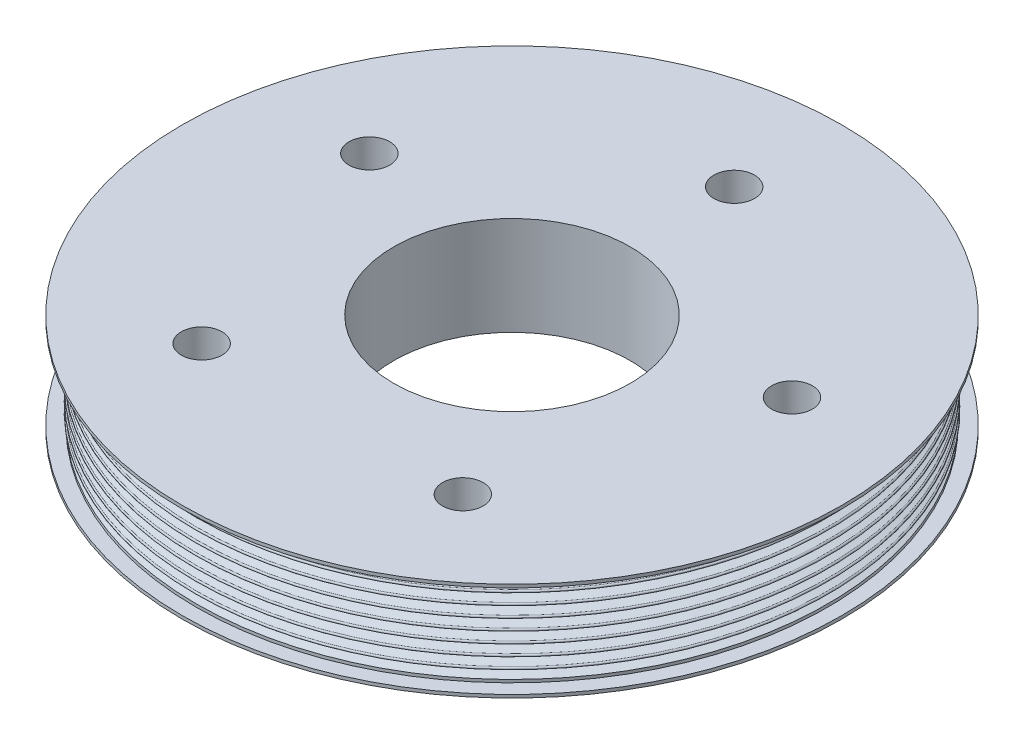
SolidWorks part; units mm, degrees
material "6061-T6 (SS)"
ref_plane "Front Plane" through (0, 0, 0) normal (0, 0, 1) x (1, 0, 0)
ref_plane "Top Plane" through (0, 0, 0) normal (0, 1, 0) x (1, 0, 0)
ref_plane "Right Plane" through (0, 0, 0) normal (1, 0, 0) x (0, 0, -1)
sketch "Sketch1" plane through (0, 0, 0) normal (0, 0, 1) x (1, 0, 0)
  line L0 (101.6, 13.904) -> (101.6, 14.8565)
  line L1 (101.6, -13.904) -> (101.6, -14.8565)
  line L2 (106.172, -15.8725) -> (101.6, -15.8725)
  line L3 (101.6, -13.904) -> (98.7876, -12.8803)
  line L4 (98.7876, -12.8803) -> (98.7876, -12.1183) construction
  line L5 (98.7876, -12.1183) -> (101.6, -11.0947)
  line L6 (101.6, -11.0947) -> (101.6, -10.3327) construction
  line L7 (101.6, -10.3327) -> (98.7876, -9.3091)
  line L8 (98.7876, -9.3091) -> (98.7876, -8.5471) construction
  line L9 (98.7876, -8.5471) -> (101.6, -7.5235)
  line L10 (101.6, -7.5235) -> (101.6, -6.7615) construction
  line L11 (101.6, -6.7615) -> (98.7876, -5.7379)
  line L12 (98.7876, -5.7379) -> (98.7876, -4.9759) construction
  line L13 (98.7876, -4.9759) -> (101.6, -3.9522)
  line L14 (101.6, -3.9522) -> (101.6, -3.1902) construction
  line L15 (101.6, -3.1902) -> (98.7876, -2.1666)
  line L16 (98.7876, -2.1666) -> (98.7876, -1.4046) construction
  line L17 (98.7876, -1.4046) -> (101.6, -0.381)
  line L18 (101.6, -0.381) -> (101.6, 0.381) construction
  line L19 (101.6, 0.381) -> (98.7876, 1.4046)
  line L20 (98.7876, 1.4046) -> (98.7876, 2.1666) construction
  line L21 (98.7876, 2.1666) -> (101.6, 3.1902)
  line L22 (101.6, 3.1902) -> (101.6, 3.9522) construction
  line L23 (101.6, 3.9522) -> (98.7876, 4.9759)
  line L24 (98.7876, 4.9759) -> (98.7876, 5.7379) construction
  line L25 (98.7876, 5.7379) -> (101.6, 6.7615)
  line L26 (101.6, 6.7615) -> (101.6, 7.5235) construction
  line L27 (101.6, 7.5235) -> (98.7876, 8.5471)
  line L28 (98.7876, 8.5471) -> (98.7876, 9.3091) construction
  line L29 (98.7876, 9.3091) -> (101.6, 10.3327)
  line L30 (101.6, 10.3327) -> (101.6, 11.0947) construction
  line L31 (101.6, 11.0947) -> (98.7876, 12.1183)
  line L32 (98.7876, 12.1183) -> (98.7876, 12.8803) construction
  line L33 (98.7876, 12.8803) -> (101.6, 13.904)
  line L34 (101.6, -15.8725) -> (0, -15.8725)
  line L35 (101.6, 15.8725) -> (0, 15.8725)
  line L36 (0, 15.8725) -> (0, -15.8725)
  line L37 (101.6, 10.7137) -> (23.534, 10.7137) construction
  line L38 (101.6, -13.904) -> (101.6, -11.0947) construction
  line L39 (106.172, -15.8725) -> (106.172, -14.8565)
  line L40 (106.172, -14.8565) -> (101.6, -14.8565)
  line L42 (101.6, 15.8725) -> (106.172, 15.8725)
  line L43 (106.172, 15.8725) -> (106.172, 14.8565)
  line L44 (106.172, 14.8565) -> (101.6, 14.8565)
  arc A0 (98.7876, 12.8803) -> (98.7876, 12.1183) centre (98.7876, 12.4993) ccw
  arc A1 (98.7876, 9.3091) -> (98.7876, 8.5471) centre (98.7876, 8.9281) ccw
  arc A2 (98.7876, 5.7379) -> (98.7876, 4.9759) centre (98.7876, 5.3569) ccw
  arc A3 (98.7876, 2.1666) -> (98.7876, 1.4046) centre (98.7876, 1.7856) ccw
  arc A4 (98.7876, -1.4046) -> (98.7876, -2.1666) centre (98.7876, -1.7856) ccw
  arc A5 (98.7876, -4.9759) -> (98.7876, -5.7379) centre (98.7876, -5.3569) ccw
  arc A6 (98.7876, -8.5471) -> (98.7876, -9.3091) centre (98.7876, -8.9281) ccw
  arc A7 (98.7876, -12.1183) -> (98.7876, -12.8803) centre (98.7876, -12.4993) ccw
  arc A8 (101.6, 11.0947) -> (101.6, 10.3327) centre (101.6, 10.7137) cw
  arc A9 (101.6, 7.5235) -> (101.6, 6.7615) centre (101.6, 7.1425) cw
  arc A10 (101.6, 3.1902) -> (101.6, 3.9522) centre (101.6, 3.5712) ccw
  arc A11 (101.6, -0.381) -> (101.6, 0.381) centre (101.6, 0) ccw
  arc A12 (101.6, -3.9522) -> (101.6, -3.1902) centre (101.6, -3.5712) ccw
  arc A13 (101.6, -7.5235) -> (101.6, -6.7615) centre (101.6, -7.1425) ccw
  arc A14 (101.6, -11.0947) -> (101.6, -10.3327) centre (101.6, -10.7137) ccw
  point P1 (0, 0)
  dimension "D9" = 0.9525
  dimension "D5" = 0.381
  dimension "D1" = 20
  dimension "D2" = 20
  dimension "D3" = 3.5712
  dimension "D4" = 101.6
  dimension "D7" = 4.572
  dimension "D8" = 1.016
revolve "Revolve1" add sketch "Sketch1" angle 360 about L36
sketch "Sketch2" plane through (0, 15.8725, 0) normal (0, 1, 0) x (1, 0, 0)
  circle A0 centre (0, 0) radius 38.1
  dimension "D1" = 76.2
extrude "Cut-Extrude1" cut sketch "Sketch2" against normal through all
sketch "Sketch6" plane through (0, 15.8725, 0) normal (0, 1, 0) x (1, 0, 0)
  circle A0 centre (0, 0) radius 43.5154
  circle A1 centre (0, 0) radius 44.45
  circle A2 centre (0, 0) radius 38.1 construction
  dimension "D1" = 6.35
extrude "Cut-Extrude2" [suppressed] cut sketch "Sketch6" against normal offset from surface (1.27 mm away) 30.48
sketch "Sketch8" plane through (0, -15.8725, 0) normal (0, -1, 0) x (1, 0, 0)
  line L0 (0, 0) -> (0, -71.5518) construction
  dimension "D1" = 71.5518
hole_wizard "1/2 Clearance Hole1" positions "Sketch10" profile "Sketch11" hole size "1/2" standard "Ansi Inch" end condition through all
sketch "Sketch10" plane through (0, -15.8725, 0) normal (0, -1, 0) x (1, 0, 0)
  point P1 (0, -71.5518)
sketch "Sketch11" plane through (0, -15.8725, -71.5518) normal (1, 0, 0) x (0, 0, -1)
  line L0 (0, 0) -> (0, 31.7449)
  line L1 (0, 31.7449) -> (6.5481, 31.7449)
  line L2 (6.5481, 31.7449) -> (6.5481, 0)
  line L5 (6.5481, 0) -> (0, 0)
  line L11 (0, -6.35) -> (0, 107.95) construction
  dimension "Thru Hole Dia." = 13.0962
  dimension "Thru Hole Depth" = 31.7449
pattern_circular "CirPattern1" count 5 over 360 about axis through (0, 0, 0) along (0, 1, 0) of "1/2 Clearance Hole1"
equation "\"D2@Sketch1\" = \"D1@Sketch1\""
